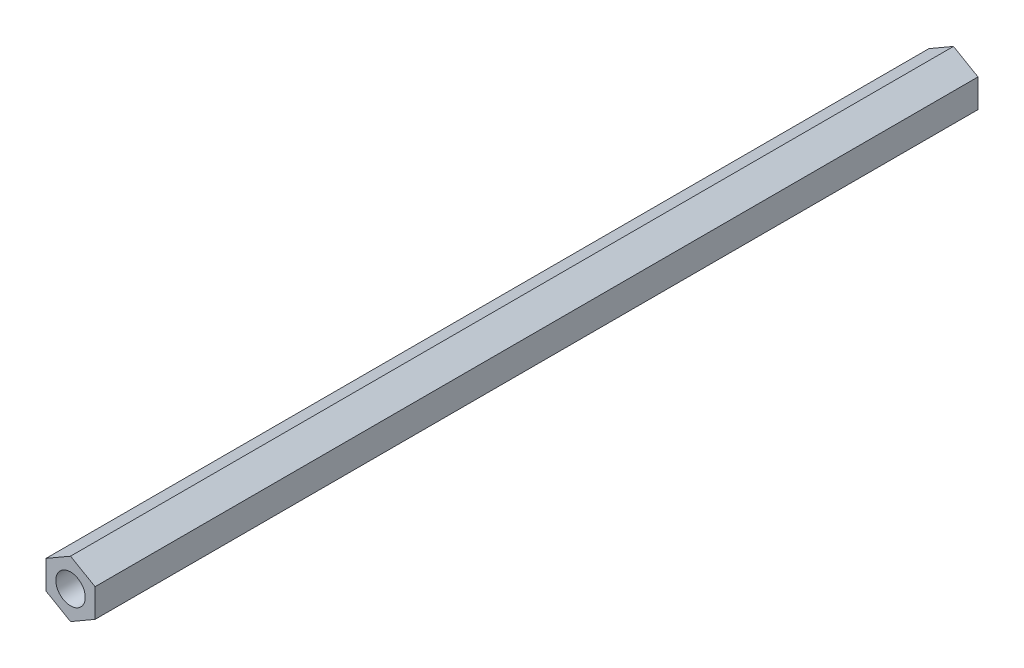
SolidWorks part; units mm, degrees
ref_plane "Plan de face" through (0, 0, 0) normal (0, 0, 1) x (1, 0, 0)
ref_plane "Plan de dessus" through (0, 0, 0) normal (0, 1, 0) x (1, 0, 0)
ref_plane "Plan de droite" through (0, 0, 0) normal (1, 0, 0) x (0, 0, -1)
sketch "Esquisse1" plane through (0, 0, 0) normal (0, 0, 1) x (1, 0, 0)
  line L1 (0, 2.8868) -> (-2.5, 1.4434)
  line L2 (-2.5, 1.4434) -> (-2.5, -1.4434)
  line L3 (-2.5, -1.4434) -> (0, -2.8868)
  line L4 (0, -2.8868) -> (2.5, -1.4434)
  line L5 (2.5, -1.4434) -> (2.5, 1.4434)
  line L6 (2.5, 1.4434) -> (0, 2.8868)
  circle A0 centre (0, 0) radius 1.5
  circle A1 centre (0, 0) radius 2.5 construction
  dimension "D1" = 3
  dimension "D2" = 1
extrude "Boss.-Extru.1" add sketch "Esquisse1" along normal blind 90
